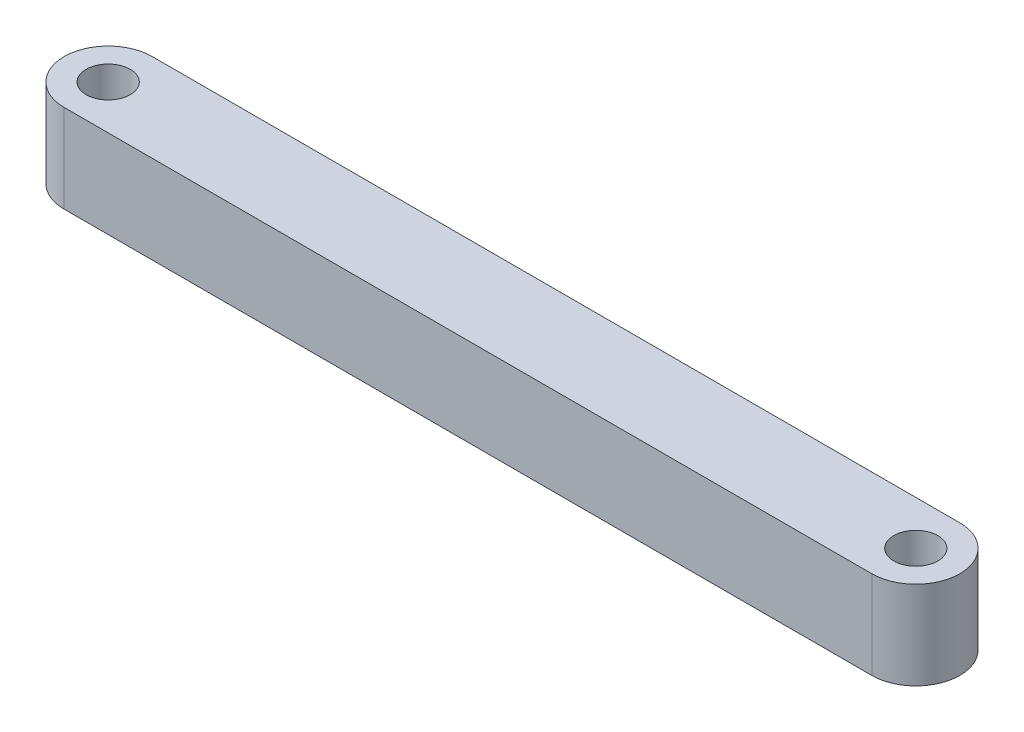
SolidWorks part; units mm, degrees
ref_plane "Front Plane" through (0, 0, 0) normal (0, 0, 1) x (1, 0, 0)
ref_plane "Top Plane" through (0, 0, 0) normal (0, 1, 0) x (1, 0, 0)
ref_plane "Right Plane" through (0, 0, 0) normal (1, 0, 0) x (0, 0, -1)
sketch "Sketch1" plane through (0, 0, 0) normal (0, 1, 0) x (1, 0, 0)
  line L0 (-27.5, 6) -> (-27.5, 0) construction
  line L1 (0, 0) -> (-55, 0)
  line L3 (0, 6) -> (-55, 6)
  arc A0 (-55, 6) -> (-55, 0) centre (-55, 3) ccw
  arc A1 (0, 6) -> (0, 0) centre (0, 3) cw
  circle A2 centre (-55, 3) radius 1.5
  circle A3 centre (0, 3) radius 1.5
  dimension "D3" = 6
  dimension "D4" = 3
  dimension "D1" = 6
  dimension "D2" = 55
extrude "Boss-Extrude1" add sketch "Sketch1" along normal blind 6
